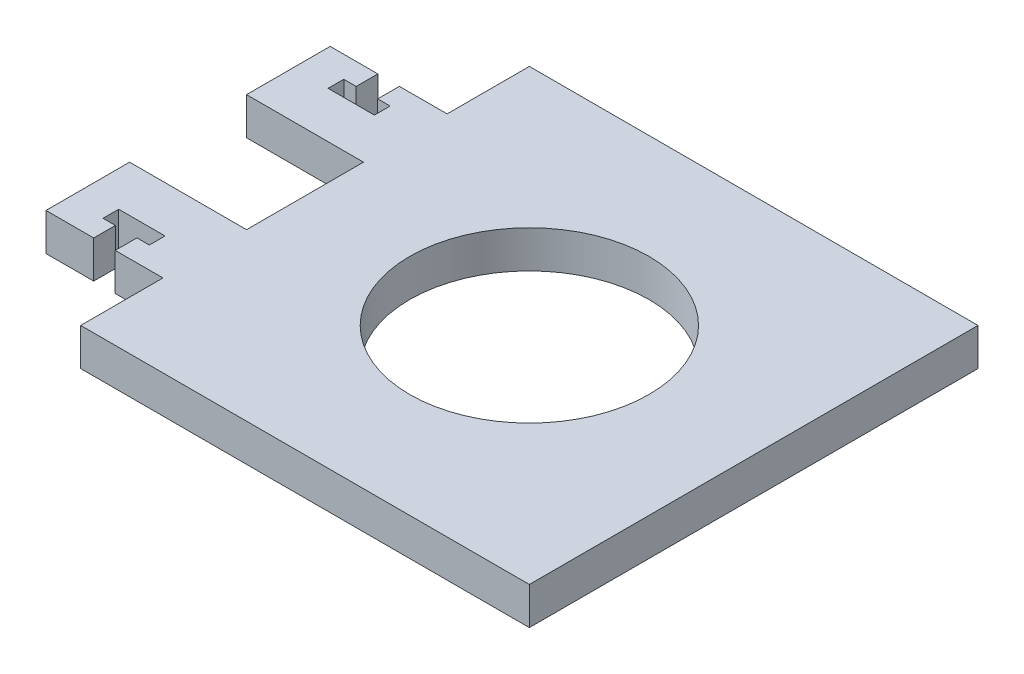
SolidWorks part; units mm, degrees
ref_plane "Front Plane" through (0, 0, 0) normal (0, 0, 1) x (1, 0, 0)
ref_plane "Top Plane" through (0, 0, 0) normal (0, 1, 0) x (1, 0, 0)
ref_plane "Right Plane" through (0, 0, 0) normal (1, 0, 0) x (0, 0, -1)
sketch "Sketch1" plane through (0, 0, 0) normal (0, 1, 0) x (1, 0, 0)
  line L0 (0, 0) -> (38.1, 0) construction
  line L1 (-38.1, -38.1) -> (38.1, -38.1)
  line L2 (-38.1, -38.1) -> (-38.1, -24.13)
  line L3 (-38.1, 38.1) -> (38.1, 38.1)
  line L4 (38.1, -38.1) -> (38.1, 38.1)
  line L5 (-38.1, -38.1) -> (38.1, 38.1) construction
  line L6 (-38.1, 38.1) -> (38.1, -38.1) construction
  line L7 (0, 0) -> (0, -18.5806) construction
  line L8 (-38.1, -24.13) -> (-46.2026, -24.13)
  line L9 (-57.9628, -24.13) -> (-57.9628, -9.9314)
  line L10 (-57.9628, -9.9314) -> (-38.1, -9.9314)
  line L12 (-38.1, 24.13) -> (-46.2026, 24.13)
  line L13 (-57.9628, 9.9314) -> (-38.1, 9.9314)
  line L14 (-57.9628, 24.13) -> (-57.9628, 9.9314)
  line L15 (-38.1, 24.13) -> (-38.1, 38.1)
  line L16 (-38.1, -9.9314) -> (-38.1, 9.9314)
  line L17 (-48.0314, -24.13) -> (-48.0314, -17.78) construction
  line L19 (-46.2026, -24.13) -> (-46.2026, -20.447)
  line L20 (-46.2026, -20.447) -> (-44.0944, -20.447)
  line L21 (-44.0944, -20.447) -> (-44.0944, -17.78)
  line L22 (-44.0944, -17.78) -> (-51.9684, -17.78)
  line L23 (-49.8602, -24.13) -> (-49.8602, -20.447)
  line L24 (-49.8602, -20.447) -> (-51.9684, -20.447)
  line L25 (-51.9684, -20.447) -> (-51.9684, -17.78)
  line L26 (-49.8602, 20.447) -> (-51.9684, 20.447)
  line L27 (-49.8602, 24.13) -> (-49.8602, 20.447)
  line L28 (-46.2026, 24.13) -> (-46.2026, 20.447)
  line L29 (-46.2026, 20.447) -> (-44.0944, 20.447)
  line L30 (-44.0944, 20.447) -> (-44.0944, 17.78)
  line L31 (-44.0944, 17.78) -> (-51.9684, 17.78)
  line L32 (-51.9684, 20.447) -> (-51.9684, 17.78)
  line L33 (-49.8602, -24.13) -> (-57.9628, -24.13)
  line L34 (-49.8602, 24.13) -> (-57.9628, 24.13)
  circle A0 centre (0, 0) radius 20.32
  point P0 (0, 0)
  point P11 (0, -18.5806)
  point P25 (0, 0)
  point P35 (0, 0)
  dimension "D2" = 40.64
  dimension "D1" = 45
  dimension "D3" = 76.2
  dimension "D4" = 13.97
  dimension "D5" = 14.1986
  dimension "D6" = 19.8628
  dimension "D7" = 7.874
  dimension "D8" = 2.667
  dimension "D9" = 6.35
  dimension "D10" = 3.6576
extrude "Boss-Extrude1" add sketch "Sketch1" against normal blind 6.35
